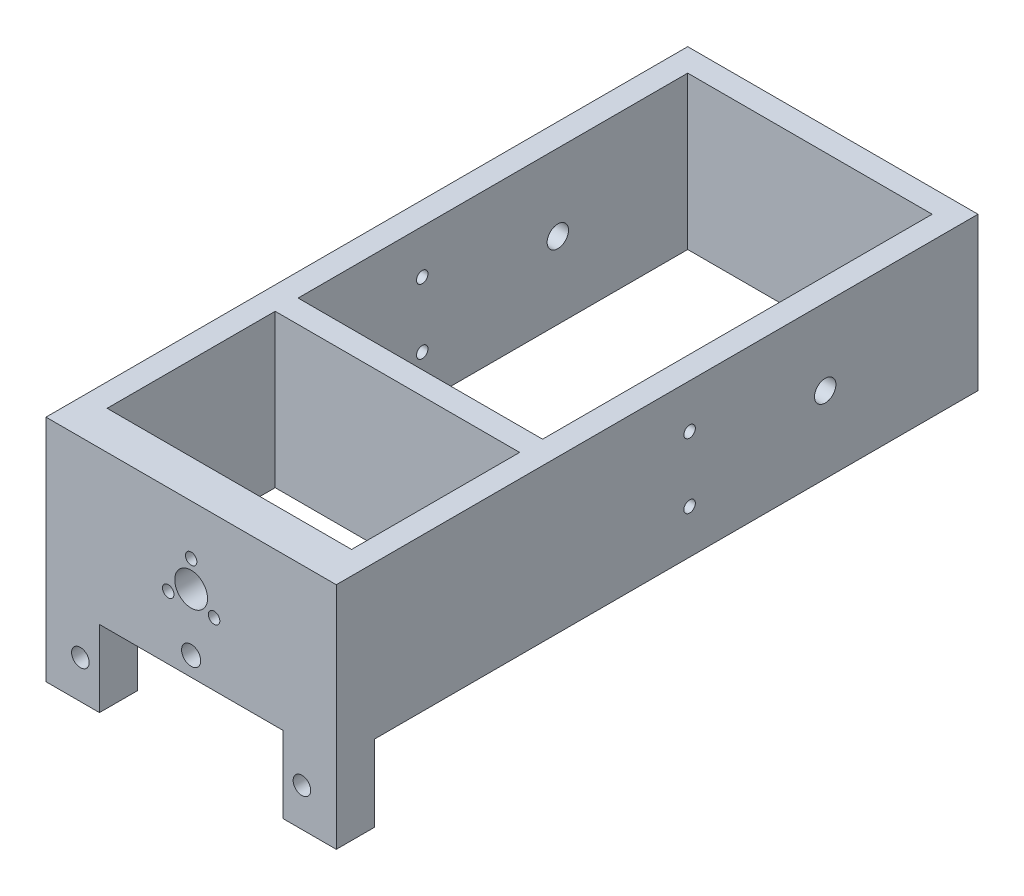
SolidWorks part; units mm, degrees
ref_plane "Plano frontal" through (0, 0, 0) normal (0, 0, 1) x (1, 0, 0)
ref_plane "Plano superior" through (0, 0, 0) normal (0, 1, 0) x (1, 0, 0)
ref_plane "Plano direito" through (0, 0, 0) normal (1, 0, 0) x (0, 0, -1)
sketch "Esboço2" plane through (0, 0, 0) normal (1, 0, 0) x (0, 0, -1)
  line L0 (55, 0) -> (-55, 0) construction
  line L2 (-44, 10) -> (40, 10)
  line L3 (-44, 10) -> (-44, -10)
  line L4 (-44, -10) -> (40, -10)
  line L5 (40, 10) -> (40, -10)
  circle A3 centre (2.25, 4.25) radius 0.75
  circle A4 centre (2.25, -4.25) radius 0.75
  circle A5 centre (20, 0) radius 1.4
  point P9 (40, 0)
  dimension "D3" = 20
  dimension "D4" = 2.8
  dimension "D5" = 20
  dimension "D1" = 1.5
  dimension "D2" = 4.25
  dimension "D6" = 2.25
  dimension "D7" = 20
  dimension "D8" = 44
extrude "Ressalto-extrusão1" add sketch "Esboço2" along normal mid plane 38
sketch "Esboço3" plane through (0, 10, 0) normal (0, 1, 0) x (1, 0, 0)
  line L0 (19, -44) -> (-19, -44) construction
  line L9 (-16, 37) -> (16, 37)
  line L10 (-16, 37) -> (-16, -14)
  line L11 (-16, -14) -> (16, -14)
  line L20 (16, 37) -> (16, -14)
  line L21 (16, -17) -> (-16, -17)
  line L22 (16, -17) -> (16, -39)
  line L23 (16, -39) -> (-16, -39)
  line L24 (-16, -17) -> (-16, -39)
  line L25 (19, 40) -> (19, -44) construction
  line L26 (19, 40) -> (-19, 40) construction
  point P10 (0, -17)
  point P11 (0, -14)
  dimension "D2" = 3
  dimension "D1" = 14
  dimension "D3" = 5
  dimension "D4" = 3
  dimension "D5" = 3
extrude "Corte-extrusão1" cut sketch "Esboço3" against normal through all
sketch "Esboço6" plane through (0, -10, 0) normal (0, -1, 0) x (1, 0, 0)
  line L0 (-16, 39) -> (16, 39) construction
  line L1 (-19, 44) -> (-12, 44)
  line L2 (-19, 44) -> (-19, 39)
  line L3 (-19, 39) -> (-12, 39)
  line L4 (-12, 44) -> (-12, 39)
  line L5 (0, -55) -> (0, 55) construction
  line L6 (19, 39) -> (12, 39)
  line L7 (12, 44) -> (12, 39)
  line L8 (19, 44) -> (12, 44)
  line L9 (19, 44) -> (19, 39)
  dimension "D1" = 12
extrude "Ressalto-extrusão2" add sketch "Esboço6" along normal blind 10
sketch "Esboço4" plane through (0, 0, 44) normal (0, 0, 1) x (1, 0, 0)
  line L0 (-3, -1.7321) -> (0, 3.4641) construction
  line L1 (0, 3.4641) -> (3, -1.7321) construction
  line L2 (3, -1.7321) -> (-3, -1.7321) construction
  line L3 (19, 10) -> (-19, 10) construction
  line L4 (12, -10) -> (-12, -10) construction
  line L5 (-12, -20) -> (-12, -10) construction
  line L6 (12, -20) -> (12, -10) construction
  line L7 (0, -55) -> (0, 55) construction
  circle A0 centre (0, 3.4641) radius 0.75
  circle A1 centre (3, -1.7321) radius 0.75
  circle A2 centre (-3, -1.7321) radius 0.75
  circle A4 centre (0, 0) radius 3.4641 construction
  circle A5 centre (0, -7.5) radius 1.25
  circle A6 centre (0, 0) radius 2.15
  circle A7 centre (-14.5, -15) radius 1.15
  circle A8 centre (14.5, -15) radius 1.15
  point P16 (0, 10)
  point P26 (12, -15)
  dimension "D2" = 1.5
  dimension "D3" = 2.5
  dimension "D5" = 4.3
  dimension "D7" = 2.3
  dimension "D1" = 6
  dimension "D4" = 2.5
  dimension "D6" = 2.5
extrude "Corte-extrusão2" cut sketch "Esboço4" against normal up to next
fillet "Filete1" [suppressed] radius 0.5
